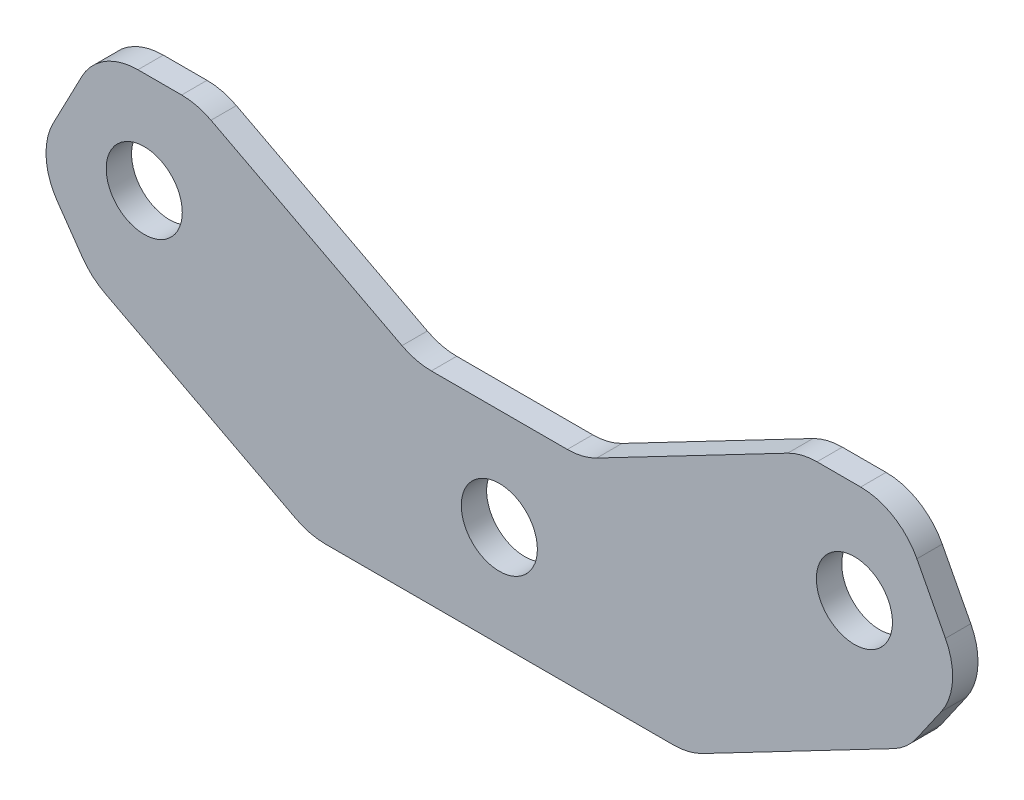
SolidWorks part; units mm, degrees
ref_plane "Front" through (0, 0, 0) normal (0, 0, 1) x (1, 0, 0)
ref_plane "Top" through (0, 0, 0) normal (0, 1, 0) x (1, 0, 0)
ref_plane "Right" through (0, 0, 0) normal (1, 0, 0) x (0, 0, -1)
sketch "Szkic1" plane through (0, 0, 0) normal (0, 0, 1) x (1, 0, 0)
  line L0 (0, 0) -> (0, -8) construction
  line L1 (0, 0) -> (0, 8) construction
  line L2 (-6.5887, 8) -> (6.5887, 8)
  line L5 (6.5887, 8) -> (23.822, 17)
  line L6 (28, 9) -> (23.822, 17) construction
  line L9 (23.822, 17) -> (31.5252, 17)
  line L10 (31.5252, 17) -> (36.5797, 7.3217)
  line L11 (36.5797, 7.3217) -> (32.178, 1)
  line L12 (6.5887, 8) -> (6.5887, -8) construction
  line L13 (6.5887, 8) -> (14.9447, -8)
  line L14 (32.178, 1) -> (14.9447, -8)
  line L15 (-14.9447, -8) -> (14.9447, -8)
  line L16 (28, 9) -> (32.178, 1)
  line L17 (28, 9) -> (34.0524, 12.1608) construction
  line L18 (-32.178, 1) -> (-14.9447, -8)
  line L19 (-36.5797, 7.3217) -> (-32.178, 1)
  line L20 (-31.5252, 17) -> (-36.5797, 7.3217)
  line L21 (-23.822, 17) -> (-31.5252, 17)
  line L22 (-6.5887, 8) -> (-23.822, 17)
  circle A0 centre (0, 0) radius 3
  circle A1 centre (28, 9) radius 3
  circle A2 centre (-28, 9) radius 3
  dimension "D1" = 6
  dimension "D2" = 6
  dimension "D3" = 6
  dimension "D4" = 8
extrude "Dodanie-wyciągnięcie1" add sketch "Szkic1" along normal blind 2
fillet "Zaokrąglenie2" radius 5 12 edges at (-32.178, 1, 1) (-14.9447, -8, 1) (14.9447, -8, 1) (32.178, 1, 1) (36.5797, 7.3217, 1) (23.822, 17, 1) (6.5887, 8, 1) (-6.5887, 8, 1) (-23.822, 17, 1) (-36.5797, 7.3217, 1) (-31.5252, 17, 1) (31.5252, 17, 1)
